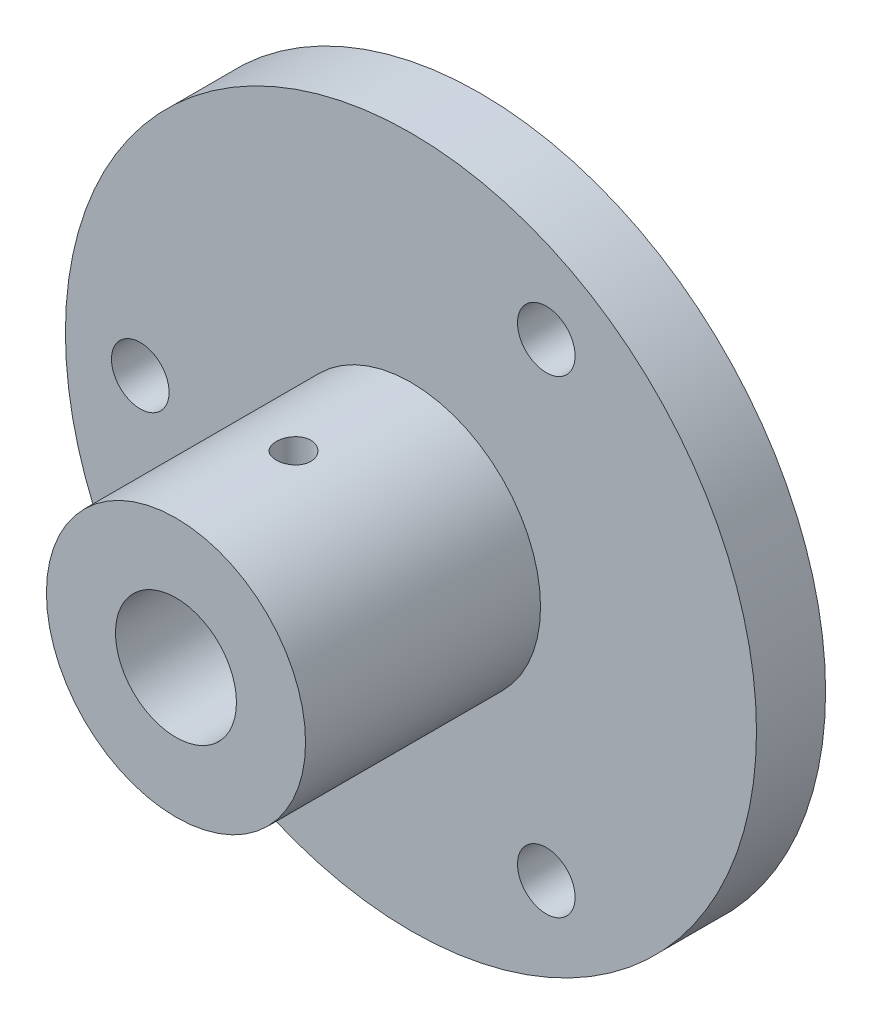
SolidWorks part; units mm, degrees
ref_plane "正面" through (0, 0, 0) normal (0, 0, 1) x (1, 0, 0)
ref_plane "平面" through (0, 0, 0) normal (0, 1, 0) x (1, 0, 0)
ref_plane "右側面" through (0, 0, 0) normal (1, 0, 0) x (0, 0, -1)
sketch "ｽｹｯﾁ1" plane through (0, 0, 0) normal (0, 0, 1) x (1, 0, 0)
  line L0 (-23.5, 0) -> (11.75, -20.3516) construction
  line L1 (11.75, -20.3516) -> (11.75, 20.3516) construction
  line L2 (11.75, 20.3516) -> (-23.5, 0) construction
  circle A0 centre (0, 0) radius 23.5 construction
  circle A2 centre (0, 0) radius 30
  circle A3 centre (-23.5, 0) radius 2.5
  circle A4 centre (11.75, -20.3516) radius 2.5
  circle A5 centre (11.75, 20.3516) radius 2.5
  circle A6 centre (0, 0) radius 5.25
  dimension "D1" = 47
  dimension "D2" = 5
  dimension "D3" = 60
  dimension "D4" = 10.5
extrude "ﾎﾞｽ - 押し出し1" add sketch "ｽｹｯﾁ1" along normal blind 6
sketch "ｽｹｯﾁ3" plane through (0, 0, 6) normal (0, 0, 1) x (1, 0, 0)
  circle A0 centre (0, 0) radius 11.25
  circle A1 centre (0, 0) radius 5.25
  circle A2 centre (0, 0) radius 5.25 construction
  dimension "D1" = 6
extrude "ﾎﾞｽ - 押し出し2" add sketch "ｽｹｯﾁ3" along normal blind 20.4
sketch "ｽｹｯﾁ4" plane through (0, 0, 0) normal (0, 1, 0) x (1, 0, 0)
  line L0 (0, -26.4) -> (0, 0) construction
  line L1 (-11.25, -26.4) -> (11.25, -26.4) construction
  circle A0 centre (0, -16.2) radius 1.5
  dimension "D1" = 10.2
  dimension "D2" = 3
extrude "ｶｯﾄ - 押し出し1" cut sketch "ｽｹｯﾁ4" along normal through all both and the other way through all
